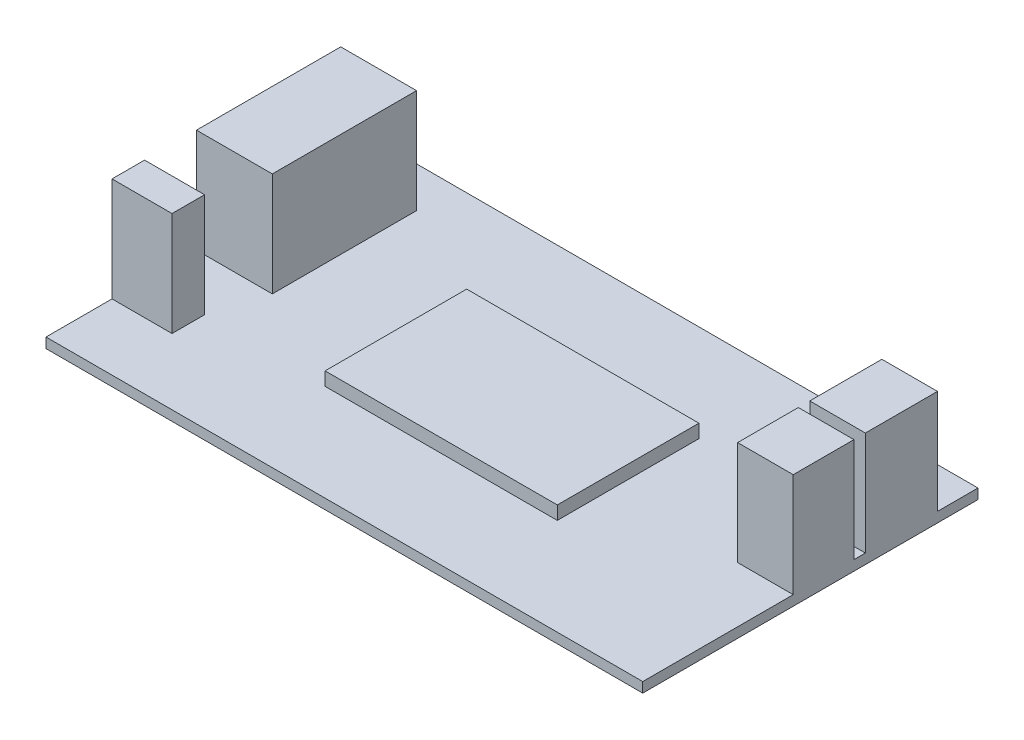
SolidWorks part; units mm, degrees
ref_plane "Front" through (0, 0, 0) normal (0, 0, 1) x (1, 0, 0)
ref_plane "Top" through (0, 0, 0) normal (0, 1, 0) x (1, 0, 0)
ref_plane "Right" through (0, 0, 0) normal (1, 0, 0) x (0, 0, -1)
sketch "Sketch1" plane through (0, 0, 0) normal (0, 1, 0) x (1, 0, 0)
  line L1 (-44.5, 25) -> (44.5, 25)
  line L2 (-44.5, 25) -> (-44.5, -25)
  line L3 (-44.5, -25) -> (44.5, -25)
  line L4 (44.5, 25) -> (44.5, -25)
  line L5 (-44.5, 25) -> (44.5, -25) construction
  line L6 (-44.5, -25) -> (44.5, 25) construction
  point P0 (0, 0)
  dimension "D1" = 89
  dimension "D2" = 50
extrude "Boss-Extrude1" add sketch "Sketch1" along normal blind 1.5
sketch "Sketch2" plane through (0, 1.5, 0) normal (0, 1, 0) x (1, 0, 0)
  line L0 (-44.5, 25) -> (-44.5, -25) construction
  line L1 (-44.5, 18.9567) -> (-33.1907, 18.9567)
  line L2 (-44.5, 18.9567) -> (-44.5, -2.5582)
  line L3 (-44.5, -2.5582) -> (-33.1907, -2.5582)
  line L4 (-33.1907, 18.9567) -> (-33.1907, -2.5582)
  line L5 (44.5, -25) -> (44.5, 25) construction
  line L6 (-44.5, -10.2983) -> (-35.552, -10.2983)
  line L7 (-44.5, -10.2983) -> (-44.5, -15.1523)
  line L8 (-44.5, -15.1523) -> (-35.552, -15.1523)
  line L9 (-35.552, -10.2983) -> (-35.552, -15.1523)
  line L10 (44.5, 18.9567) -> (36.208, 18.9567)
  line L11 (44.5, 18.9567) -> (44.5, 8.1993)
  line L12 (44.5, 8.1993) -> (36.208, 8.1993)
  line L13 (36.208, 18.9567) -> (36.208, 8.1993)
  line L15 (44.5, 6.4938) -> (36.208, 6.4938)
  line L16 (44.5, 6.4938) -> (44.5, -2.5582)
  line L17 (44.5, -2.5582) -> (36.208, -2.5582)
  line L18 (36.208, 6.4938) -> (36.208, -2.5582)
extrude "Boss-Extrude2" add sketch "Sketch2" along normal blind 15.5
sketch "Sketch3" plane through (0, 1.5, 0) normal (0, 1, 0) x (1, 0, 0)
  line L1 (-17.3168, 10.5607) -> (17.3168, 10.5607)
  line L2 (-17.3168, 10.5607) -> (-17.3168, -10.5607)
  line L3 (-17.3168, -10.5607) -> (17.3168, -10.5607)
  line L4 (17.3168, 10.5607) -> (17.3168, -10.5607)
  line L5 (-17.3168, 10.5607) -> (17.3168, -10.5607) construction
  line L6 (-17.3168, -10.5607) -> (17.3168, 10.5607) construction
  point P0 (0, 0)
extrude "Boss-Extrude3" add sketch "Sketch3" along normal blind 2
